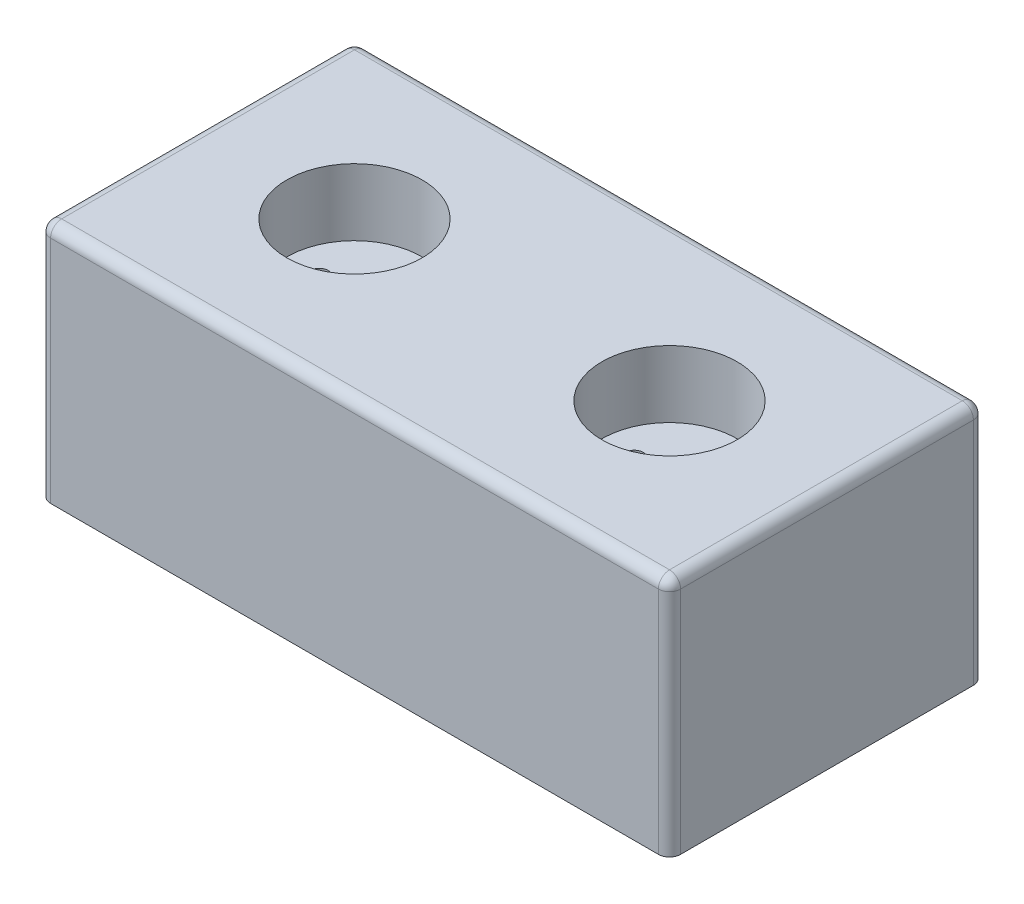
SolidWorks part; units mm, degrees
ref_plane "Спереди" through (0, 0, 0) normal (0, 0, 1) x (1, 0, 0)
ref_plane "Сверху" through (0, 0, 0) normal (0, 1, 0) x (1, 0, 0)
ref_plane "Справа" through (0, 0, 0) normal (1, 0, 0) x (0, 0, -1)
sketch "Эскиз1" plane through (0, 0, 0) normal (0, 1, 0) x (1, 0, 0)
  line L1 (85, -42.5) -> (-85, -42.5)
  line L2 (85, -42.5) -> (85, 42.5)
  line L3 (85, 42.5) -> (-85, 42.5)
  line L4 (-85, -42.5) -> (-85, 42.5)
  line L5 (85, -42.5) -> (-85, 42.5) construction
  line L6 (85, 42.5) -> (-85, -42.5) construction
  point P0 (0, 0)
  dimension "D1" = 85
  dimension "D2" = 170
extrude "Бобышка-Вытянуть1" add sketch "Эскиз1" along normal blind 65
sketch "Эскиз2" plane through (0, 65, 0) normal (0, 1, 0) x (1, 0, 0)
  line L0 (-42.5, 0) -> (42.5, 0) construction
  circle A0 centre (-42.5, 0) radius 18.25
  circle A1 centre (42.5, 0) radius 18.25
  point P3 (0, 0)
  dimension "D2" = 36.5
  dimension "D1" = 85
extrude "Вырез-Вытянуть1" cut sketch "Эскиз2" against normal blind 18
sketch "Эскиз3" plane through (0, 47, 0) normal (0, 1, 0) x (1, 0, 0)
  line L0 (-60.75, 0) -> (60.75, 0) construction
  line L1 (-42.5, 18.25) -> (-42.5, -18.25) construction
  line L2 (42.5, 18.25) -> (42.5, -18.25) construction
  circle A0 centre (-42.5, 0) radius 18.25 construction
  circle A1 centre (-42.5, 0) radius 18.25 construction
  circle A2 centre (42.5, 0) radius 18.25 construction
  circle A3 centre (42.5, 0) radius 18.25 construction
  circle A4 centre (-52, 0) radius 2.4
  circle A5 centre (-33, 0) radius 2.4
  circle A6 centre (33, 0) radius 2.4
  circle A7 centre (52, 0) radius 2.4
  dimension "D1" = 4.8
  dimension "D2" = 9.5
  dimension "D3" = 9.5
  dimension "D4" = 9.5
  dimension "D5" = 9.5
extrude "Вырез-Вытянуть2" cut sketch "Эскиз3" against normal blind 15
fillet "Скругление1" radius 3 8 edges at (85, 32.5, -42.5) (-85, 32.5, -42.5) (85, 32.5, 42.5) (-85, 32.5, 42.5) (85, 65, 0) (0, 65, -42.5) (-85, 65, 0) (0, 65, 42.5)
